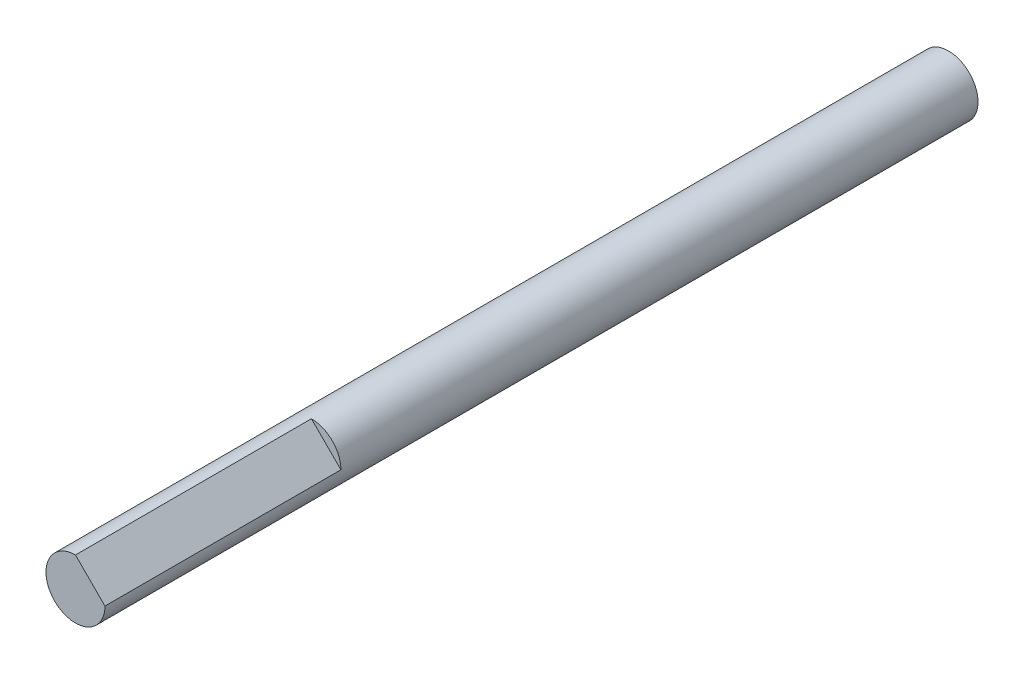
SolidWorks part; units mm, degrees
ref_plane "Front Plane" through (0, 0, 0) normal (0, 0, 1) x (1, 0, 0)
ref_plane "Top Plane" through (0, 0, 0) normal (0, 1, 0) x (1, 0, 0)
ref_plane "Right Plane" through (0, 0, 0) normal (1, 0, 0) x (0, 0, -1)
sketch "Sketch1" plane through (0, 0, 0) normal (0, 0, 1) x (1, 0, 0)
  line L1 (21.15, -21.15) -> (-21.15, -21.15)
  line L2 (21.15, -21.15) -> (21.15, 21.15)
  line L3 (21.15, 21.15) -> (-21.15, 21.15)
  line L4 (-21.15, -21.15) -> (-21.15, 21.15)
  line L5 (21.15, -21.15) -> (-21.15, 21.15) construction
  line L6 (21.15, 21.15) -> (-21.15, -21.15) construction
  point P0 (0, 0)
  dimension "D1" = 42.3
  dimension "D2" = 42.3
extrude "Boss-Extrude1" add sketch "Sketch1" along normal blind 50
sketch "Sketch2" plane through (0, 0, 50) normal (0, 0, 1) x (1, 0, 0)
  circle A0 centre (0, 0) radius 11
  dimension "D1" = 22
extrude "Boss-Extrude2" add sketch "Sketch2" along normal blind 2
sketch "Sketch3" plane through (0, 0, 50) normal (0, 0, 1) x (1, 0, 0)
  line L1 (16.55, -16.55) -> (-16.55, -16.55) construction
  line L2 (16.55, -16.55) -> (16.55, 16.55) construction
  line L3 (16.55, 16.55) -> (-16.55, 16.55) construction
  line L4 (-16.55, -16.55) -> (-16.55, 16.55) construction
  line L5 (16.55, -16.55) -> (-16.55, 16.55) construction
  line L6 (16.55, 16.55) -> (-16.55, -16.55) construction
  circle A0 centre (-16.55, 16.55) radius 1.75
  circle A1 centre (16.55, 16.55) radius 1.75
  circle A2 centre (16.55, -16.55) radius 1.75
  circle A3 centre (-16.55, -16.55) radius 1.75
  point P0 (0, 0)
  point P16 (0, 0)
  dimension "D3" = 3.5
  dimension "D1" = 33.1
  dimension "D2" = 33.1
  dimension "D4" = 4
extrude "Cut-Extrude1" cut sketch "Sketch3" against normal through all
sketch "Sketch4" plane through (0, 0, 50) normal (0, 0, 1) x (1, 0, 0)
  line L0 (-16.55, 16.55) -> (-21.15, 21.15) construction
  line L1 (-21.15, 17.8973) -> (-21.15, 21.15)
  line L2 (-21.15, 21.15) -> (-17.8973, 21.15)
  line L3 (-17.8973, 21.15) -> (-21.15, 17.8973)
  line L4 (17.8973, 21.15) -> (21.15, 21.15)
  line L5 (21.15, 21.15) -> (21.15, 17.8973)
  line L6 (21.15, 17.8973) -> (17.8973, 21.15)
  line L7 (21.15, -17.8973) -> (21.15, -21.15)
  line L8 (21.15, -21.15) -> (17.8973, -21.15)
  line L9 (17.8973, -21.15) -> (21.15, -17.8973)
  line L10 (-17.8973, -21.15) -> (-21.15, -21.15)
  line L11 (-21.15, -21.15) -> (-21.15, -17.8973)
  line L12 (-21.15, -17.8973) -> (-17.8973, -21.15)
  circle A0 centre (-21.15, 21.15) radius 3.2527 construction
  point P3 (-18.85, 18.85)
  point P20 (0, 0)
  dimension "D1" = 4
extrude "Cut-Extrude2" cut sketch "Sketch4" against normal through all
sketch "Sketch5" plane through (0, 0, 52) normal (0, 0, 1) x (1, 0, 0)
  circle A0 centre (0, 0) radius 2.5
  dimension "D1" = 5
ref_plane "Plane1" through (0, 0, 7.5) normal (0, 0, 1) x (1, 0, 0)
extrude "Cut-Extrude3" cut sketch "Sketch5" against normal through all
sketch "Sketch6" plane through (0, 0, 52) normal (0, 0, 1) x (1, 0, 0)
  circle A0 centre (0, 0) radius 2.5
  dimension "D1" = 5
extrude "Boss-Extrude3" add sketch "Sketch6" along normal blind 22 and the other way through all
sketch "Sketch7" plane through (0, 0, 0) normal (0, 0, -1) x (-1, 0, 0)
  circle A0 centre (0, 0) radius 5
  circle A1 centre (0, 0) radius 2.5
  dimension "D1" = 10
extrude "Cut-Extrude4" cut sketch "Sketch7" against normal blind 5
sketch "Sketch8" plane through (0, 0, 74) normal (0, 0, 1) x (1, 0, 0)
  line L0 (2.5, 0) -> (0, 2.5)
  arc A0 (2.5, 0) -> (0, 2.5) centre (0, 0) ccw
extrude "Cut-Extrude5" cut sketch "Sketch8" against normal blind 20
sketch "Sketch9" plane through (0, 0, 74) normal (0, 0, 1) x (1, 0, 0)
  circle A0 centre (0, 0) radius 2.5
  dimension "D1" = 5
extrude "Cut-Extrude6" cut sketch "Sketch9" against normal through all flip side to cut
